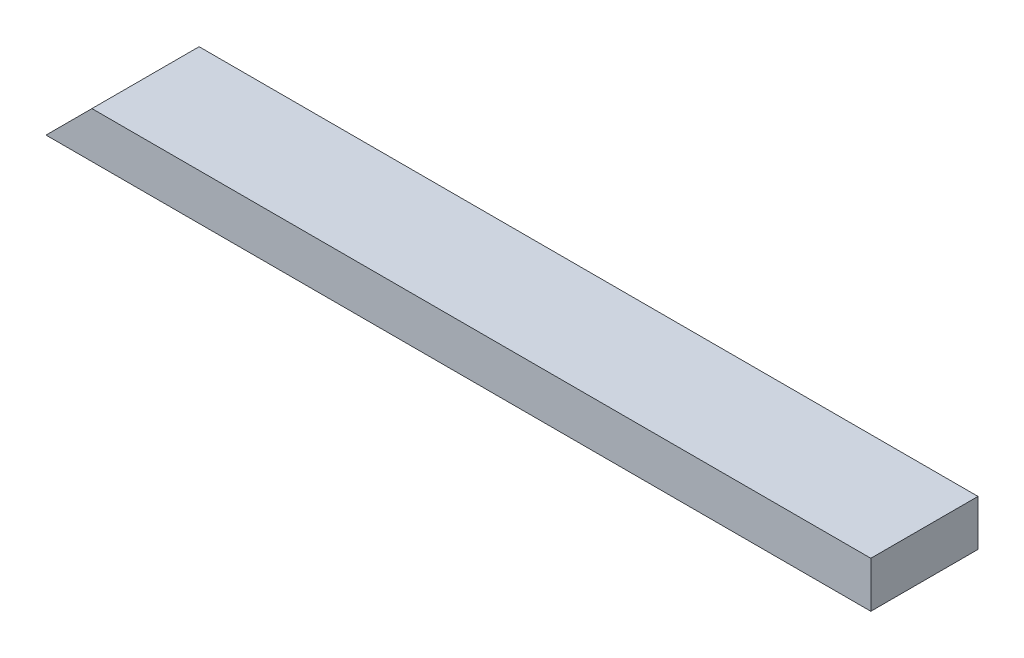
SolidWorks part; units mm, degrees
material "Pine"
ref_plane "Front Plane" through (0, 0, 0) normal (0, 0, 1) x (1, 0, 0)
ref_plane "Top Plane" through (0, 0, 0) normal (0, 1, 0) x (1, 0, 0)
ref_plane "Right Plane" through (0, 0, 0) normal (1, 0, 0) x (0, 0, -1)
sketch "Sketch1" plane through (0, 0, 0) normal (0, 1, 0) x (1, 0, 0)
  line L1 (0, 0) -> (684.2125, 0)
  line L2 (0, 0) -> (0, 88.9)
  line L3 (0, 88.9) -> (684.2125, 88.9)
  line L4 (684.2125, 0) -> (684.2125, 88.9)
  dimension "D1" = 88.9
  dimension "D2" = 684.2125
extrude "Boss-Extrude1" add sketch "Sketch1" along normal blind 38.1
sketch "Sketch2" plane through (0, 0, 0) normal (0, 0, 1) x (1, 0, 0)
  line L0 (0, 0) -> (38.1, 38.1)
  line L1 (0, 38.1) -> (684.2125, 38.1) construction
  line L2 (0, 38.1) -> (0, 0)
  line L6 (38.1, 38.1) -> (0, 38.1)
  dimension "D1" = 38.1
extrude "Cut-Extrude1" cut sketch "Sketch2" against normal through all
